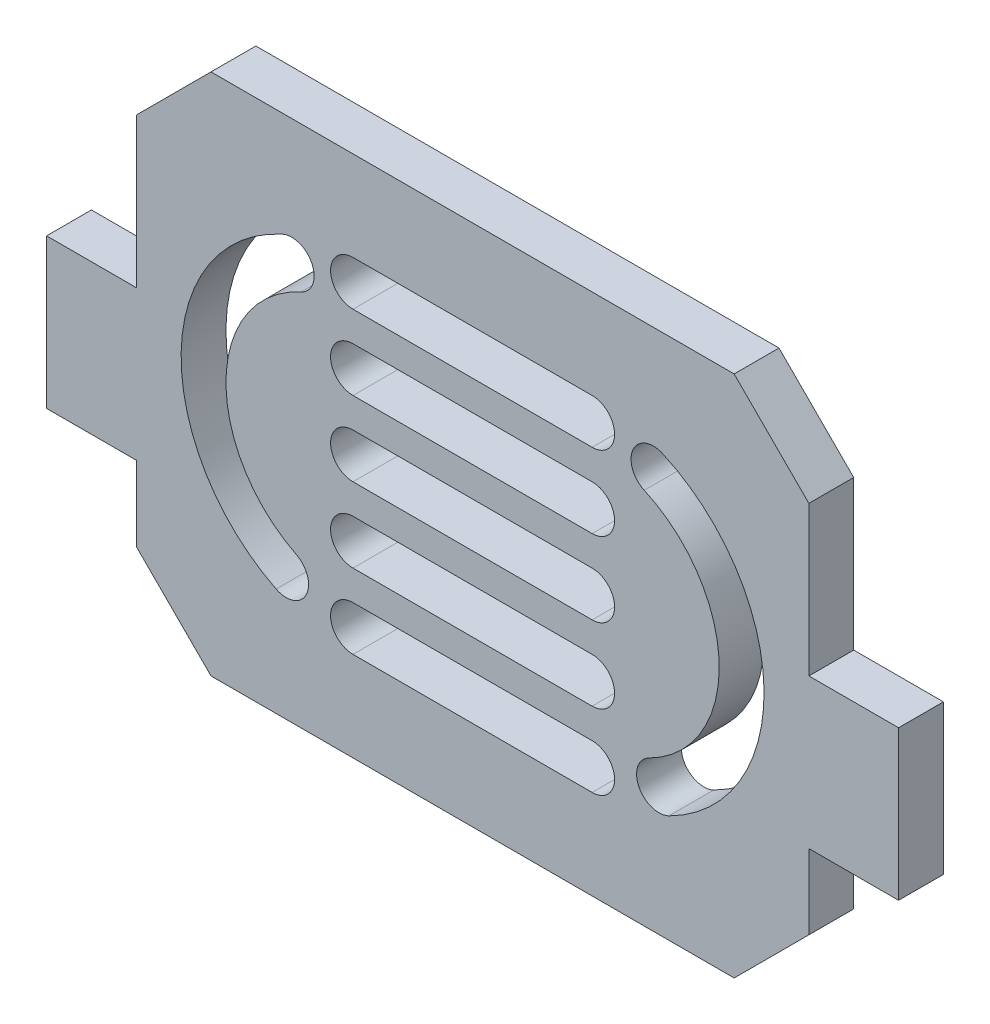
SolidWorks part; units mm, degrees
ref_plane "Front" through (0, 0, 0) normal (0, 0, 1) x (1, 0, 0)
ref_plane "Top" through (0, 0, 0) normal (0, 1, 0) x (1, 0, 0)
ref_plane "Right" through (0, 0, 0) normal (1, 0, 0) x (0, 0, -1)
sketch "Sketch1" plane through (0, 0, 0) normal (0, 0, 1) x (1, 0, 0)
  line L0 (22.5, -7.5) -> (22.5, -17.5)
  line L1 (-22.5, 17.5) -> (22.5, 17.5)
  line L2 (-22.5, 17.5) -> (-22.5, 2.5)
  line L3 (-22.5, -17.5) -> (22.5, -17.5)
  line L4 (22.5, 17.5) -> (22.5, 2.5)
  line L5 (-22.5, 17.5) -> (22.5, -17.5) construction
  line L6 (-22.5, -17.5) -> (22.5, 17.5) construction
  line L7 (22.5, 2.5) -> (28.5, 2.5)
  line L8 (-22.5, -7.5) -> (-22.5, -17.5)
  line L9 (22.5, -7.5) -> (28.5, -7.5)
  line L10 (28.5, 2.5) -> (28.5, -7.5)
  line L13 (-28.5, 2.5) -> (-22.5, 2.5)
  line L14 (-28.5, 2.5) -> (-28.5, -7.5)
  line L15 (-28.5, -7.5) -> (-22.5, -7.5)
  line L17 (-28.5, 2.5) -> (-23.5, -2.5) construction
  line L18 (-28.5, -7.5) -> (-23.5, -2.5) construction
  point P0 (0, 0)
  point P6 (22.5, 0)
  point P11 (-23.5, -2.5)
  dimension "D1" = 45
  dimension "D2" = 6
  dimension "D3" = 10
  dimension "D4" = 6
  dimension "D5" = 10
  dimension "D6" = 10
  dimension "D7" = 15
  dimension "D8" = 15
extrude "Boss-Extrude1" add sketch "Sketch1" along normal blind 3
chamfer "Chamfer1" distance 5 angle 45 4 edges at (-22.5, 17.5, 1.5) (22.5, 17.5, 1.5) (-22.5, -17.5, 1.5) (22.5, -17.5, 1.5)
sketch "Sketch2" plane through (0, 0, 3) normal (0, 0, 1) x (1, 0, 0)
  line L0 (0, 0) -> (0, 9.1206) construction
  line L1 (-8, 0) -> (8, 0) construction
  line L2 (-8, 1.5) -> (8, 1.5)
  line L3 (-8, -1.5) -> (8, -1.5)
  line L4 (-8, 5) -> (8, 5) construction
  line L5 (-8, 6.5) -> (8, 6.5)
  line L6 (-8, 3.5) -> (8, 3.5)
  line L7 (-8, 10) -> (8, 10) construction
  line L8 (-8, 11.5) -> (8, 11.5)
  line L9 (-8, 8.5) -> (8, 8.5)
  line L10 (-8, -5) -> (8, -5) construction
  line L11 (-8, -3.5) -> (8, -3.5)
  line L12 (-8, -6.5) -> (8, -6.5)
  line L13 (-8, -10) -> (8, -10) construction
  line L14 (-8, -8.5) -> (8, -8.5)
  line L15 (-8, -11.5) -> (8, -11.5)
  arc A0 (-12.1006, 9.1206) -> (-12.4725, -8.9441) centre (-8, 0) ccw construction
  arc A1 (-12.7157, 10.4887) -> (-13.1434, -10.2857) centre (-8, 0) ccw
  arc A2 (-11.4855, 7.7525) -> (-11.8016, -7.6025) centre (-8, 0) ccw
  arc A3 (-11.4855, 7.7525) -> (-12.7157, 10.4887) centre (-12.1006, 9.1206) ccw
  arc A4 (-13.1434, -10.2857) -> (-11.8016, -7.6025) centre (-12.4725, -8.9441) ccw
  arc A5 (12.1006, 9.1206) -> (12.4725, -8.9441) centre (8, 0) cw construction
  arc A6 (12.7157, 10.4887) -> (13.1434, -10.2857) centre (8, 0) cw
  arc A7 (11.4855, 7.7525) -> (11.8016, -7.6025) centre (8, 0) cw
  arc A8 (11.4855, 7.7525) -> (12.7157, 10.4887) centre (12.1006, 9.1206) cw
  arc A9 (13.1434, -10.2857) -> (11.8016, -7.6025) centre (12.4725, -8.9441) cw
  arc A10 (-8, 1.5) -> (-8, -1.5) centre (-8, 0) ccw
  arc A11 (8, -1.5) -> (8, 1.5) centre (8, 0) ccw
  arc A12 (-8, 6.5) -> (-8, 3.5) centre (-8, 5) ccw
  arc A13 (8, 3.5) -> (8, 6.5) centre (8, 5) ccw
  arc A14 (-8, 11.5) -> (-8, 8.5) centre (-8, 10) ccw
  arc A15 (8, 8.5) -> (8, 11.5) centre (8, 10) ccw
  arc A16 (-8, -3.5) -> (-8, -6.5) centre (-8, -5) ccw
  arc A17 (8, -6.5) -> (8, -3.5) centre (8, -5) ccw
  arc A18 (-8, -8.5) -> (-8, -11.5) centre (-8, -10) ccw
  arc A19 (8, -11.5) -> (8, -8.5) centre (8, -10) ccw
  point P4 (-17.9979, 0.2058)
  point P14 (17.9979, 0.2058)
  point P21 (0, 0)
  point P30 (0, 5)
  point P37 (0, 10)
  point P43 (0, -5)
  point P50 (0, -10)
  point P80 (0, -15)
  point P87 (0, -15)
  point P94 (0, -15)
  dimension "D2" = 1.5
  dimension "D4" = 1.5
  dimension "D3" = 10
  dimension "D1" = 8
  dimension "D5" = 3
  dimension "D6" = 3
extrude "Cut-Extrude1" cut sketch "Sketch2" against normal blind 5
